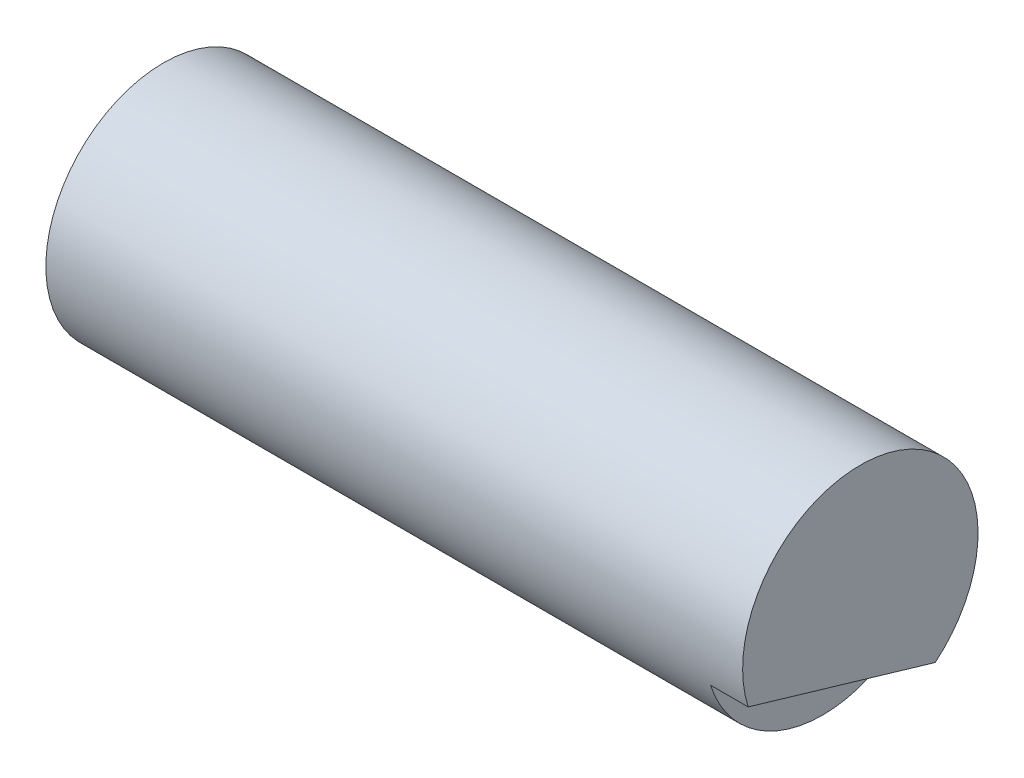
SolidWorks part; units mm, degrees
material "AISI 1045 钢，冷拔"
ref_plane "前视基准面" through (0, 0, 0) normal (0, 0, 1) x (1, 0, 0)
ref_plane "上视基准面" through (0, 0, 0) normal (0, 1, 0) x (1, 0, 0)
ref_plane "右视基准面" through (0, 0, 0) normal (1, 0, 0) x (0, 0, -1)
sketch "草图1" plane through (-5, 0, 0) normal (-1, 0, 0) x (0, 0, 1)
  circle A0 centre (-2475, 109.9502) radius 12.5
extrude "凸台-拉伸1" add sketch "草图1" against normal blind 74
sketch "草图2" plane through (-5, 0, 0) normal (-1, 0, 0) x (0, 0, 1)
  circle A0 centre (-2475, 109.9502) radius 16.5
  circle A1 centre (-2475, 109.9502) radius 12.5 construction
  dimension "D1" = 4
sketch "草图3" plane through (65, 0, 0) normal (1, 0, 0) x (0, 0, -1)
  line L0 (2482.9587, 100.3112) -> (2463.0889, 106.1586)
  circle A0 centre (2475, 109.9502) radius 12.5 construction
  arc A1 (2463.0889, 106.1586) -> (2482.9587, 100.3112) centre (2475, 109.9502) ccw
  dimension "D1" = 7
extrude "切除-拉伸1" cut sketch "草图3" along normal blind 4
